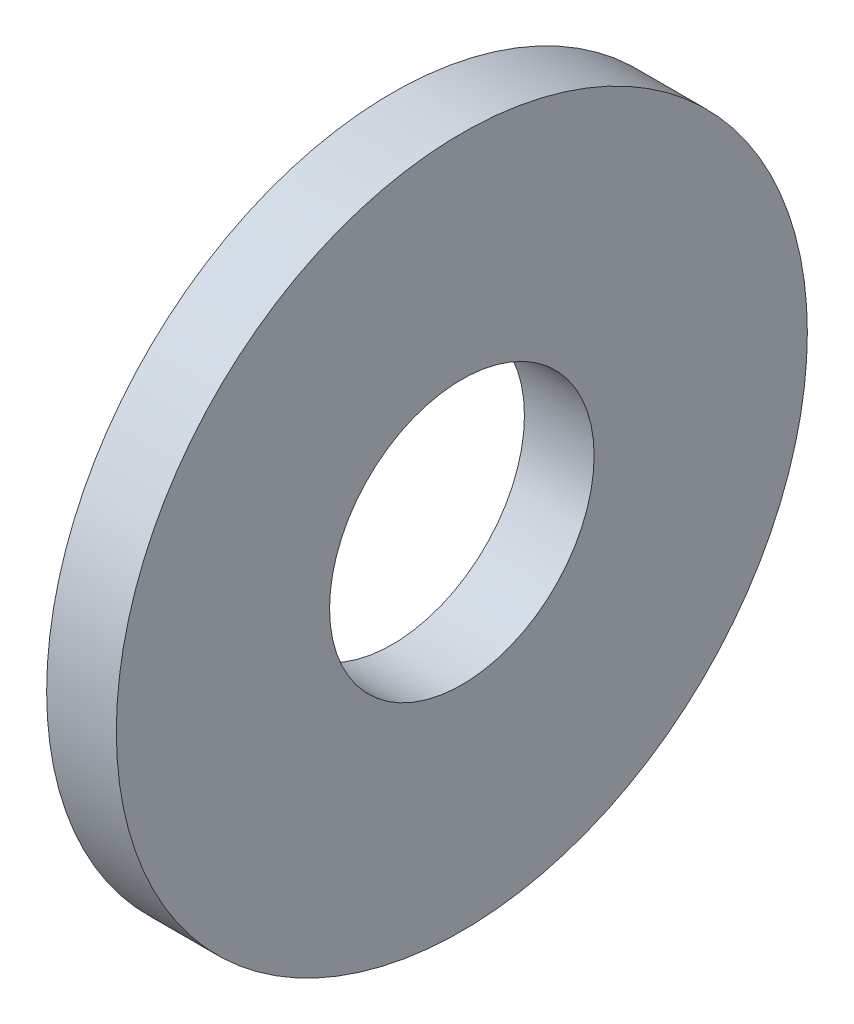
SolidWorks part; units mm, degrees
ref_plane "Front Plane" through (0, 0, 0) normal (0, 0, 1) x (1, 0, 0)
ref_plane "Top Plane" through (0, 0, 0) normal (0, 1, 0) x (1, 0, 0)
ref_plane "Right Plane" through (0, 0, 0) normal (1, 0, 0) x (0, 0, -1)
sketch "Sketch1" plane through (0, 0, 0) normal (1, 0, 0) x (0, 0, -1)
  circle A0 centre (0, 0) radius 9.3218
  circle A1 centre (0, 0) radius 3.5687
  dimension "OD" = 18.6436
  dimension "ID" = 7.1374
extrude "Boss-Extrude1" add sketch "Sketch1" along normal blind 1.8796
